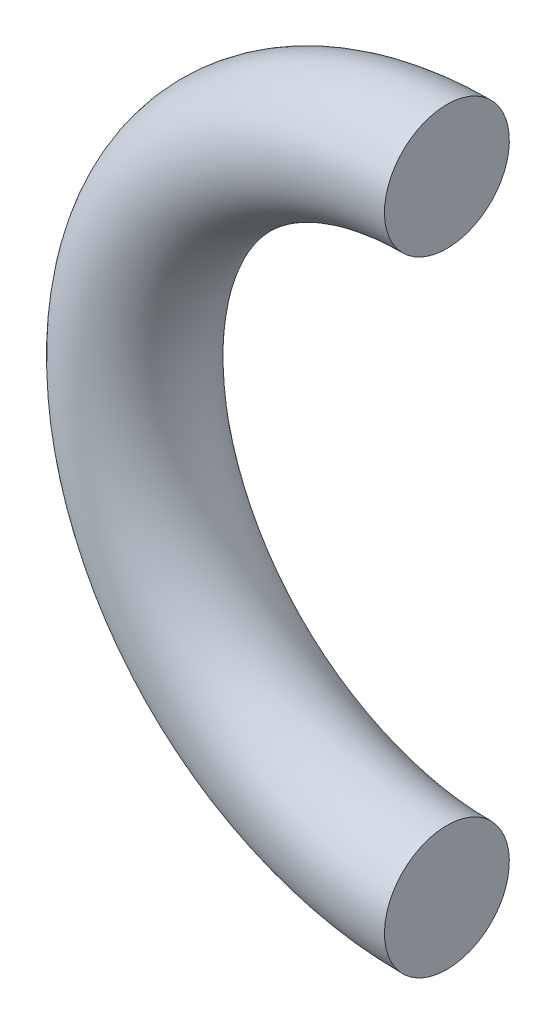
SolidWorks part; units mm, degrees
ref_plane "Front Plane" through (0, 0, 0) normal (0, 0, 1) x (1, 0, 0)
ref_plane "Top Plane" through (0, 0, 0) normal (0, 1, 0) x (1, 0, 0)
ref_plane "Right Plane" through (0, 0, 0) normal (1, 0, 0) x (0, 0, -1)
sketch "Sketch1" plane through (0, 0, 0) normal (1, 0, 0) x (0, 0, -1)
  line L0 (0, 0) -> (0, -15.875)
  line L1 (0, -15.875) -> (-25.4, -15.875)
  circle A0 centre (0, 0) radius 3.175
  dimension "D1" = 6.35
  dimension "D2" = 15.875
  dimension "D3" = 25.4
revolve "Revolve1" add sketch "Sketch1" angle 180 about L1
